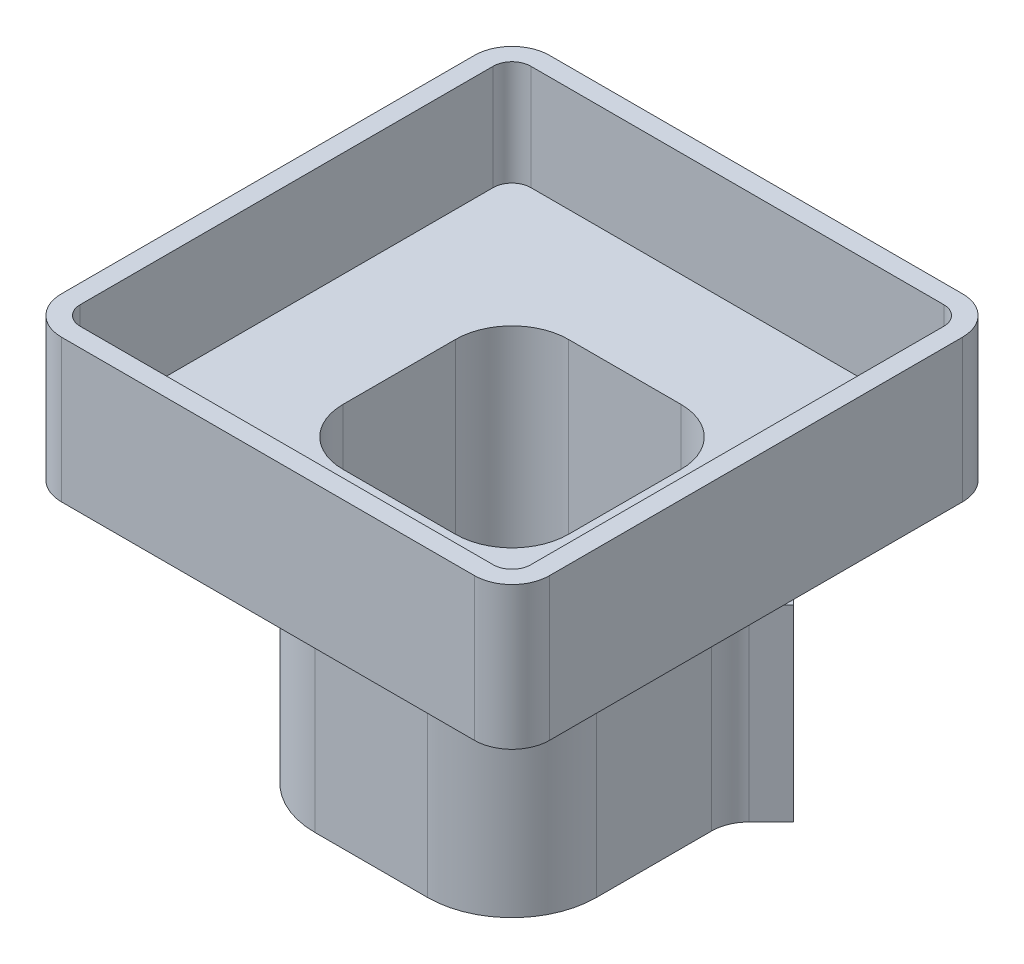
SolidWorks part; units mm, degrees
ref_plane "Front Plane" through (0, 0, 0) normal (0, 0, 1) x (1, 0, 0)
ref_plane "Top Plane" through (0, 0, 0) normal (0, 1, 0) x (1, 0, 0)
ref_plane "Right Plane" through (0, 0, 0) normal (1, 0, 0) x (0, 0, -1)
sketch "Sketch1" plane through (0, 0, 0) normal (0, 1, 0) x (1, 0, 0)
  line L1 (-3.75, 3.75) -> (3.75, 3.75)
  line L2 (-3.75, 3.75) -> (-3.75, -3.75)
  line L3 (-3.75, -3.75) -> (3.75, -3.75)
  line L4 (3.75, 3.75) -> (3.75, -3.75)
  line L5 (-3.75, 3.75) -> (3.75, -3.75) construction
  line L6 (-3.75, -3.75) -> (3.75, 3.75) construction
  dimension "D2" = 7.5
extrude "Boss-Extrude1" add sketch "Sketch1" along normal blind 7
sketch "Sketch2" plane through (0, 7, 0) normal (0, 1, 0) x (1, 0, 0)
  line L1 (6.5, 6.5) -> (-6.5, 6.5)
  line L2 (6.5, 6.5) -> (6.5, -6.5)
  line L3 (6.5, -6.5) -> (-6.5, -6.5)
  line L4 (-6.5, 6.5) -> (-6.5, -6.5)
  line L5 (6.5, 6.5) -> (-6.5, -6.5) construction
  line L6 (6.5, -6.5) -> (-6.5, 6.5) construction
  point P0 (0, 0)
  dimension "D1" = 13
  dimension "D2" = 13
extrude "Boss-Extrude2" add sketch "Sketch2" along normal blind 3.8
sketch "Sketch3" plane through (0, 0, 0) normal (0, -1, 0) x (1, 0, 0)
  line L1 (-3, -3) -> (3, -3)
  line L2 (-3, -3) -> (-3, 3)
  line L3 (-3, 3) -> (3, 3)
  line L4 (3, -3) -> (3, 3)
  line L5 (-3, -3) -> (3, 3) construction
  line L6 (-3, 3) -> (3, -3) construction
  dimension "D2" = 6
extrude "Cut-Extrude1" cut sketch "Sketch3" against normal through all
sketch "Sketch6" plane through (0, 10.8, 0) normal (0, 1, 0) x (1, 0, 0)
  line L1 (6, 6) -> (-6, 6)
  line L2 (6, 6) -> (6, -6)
  line L3 (6, -6) -> (-6, -6)
  line L4 (-6, 6) -> (-6, -6)
  line L5 (6, 6) -> (-6, -6) construction
  line L6 (6, -6) -> (-6, 6) construction
  point P0 (0, 0)
  dimension "D1" = 12
  dimension "D2" = 12
extrude "Cut-Extrude3" cut sketch "Sketch6" against normal offset from surface (2.8 mm away) 1 up to face at (0, 7, 0)
fillet "Fillet1" radius 0.5 4 edges at (-6, 9.4, -6) (6, 9.4, -6) (6, 9.4, 6) (-6, 9.4, 6)
sketch "Sketch12" plane through (0, 0, 0) normal (0, -1, 0) x (1, 0, 0)
  line L0 (4.6339, -2.8661) -> (3.75, -1.9822)
  line L1 (3.75, 3.75) -> (3.75, -3.75) construction
  line L2 (3.75, -1.9822) -> (1.9822, -3.75)
  line L3 (3.75, -3.75) -> (-3.75, -3.75) construction
  line L4 (1.9822, -3.75) -> (2.8661, -4.6339)
  line L5 (2.8661, -4.6339) -> (4.6339, -2.8661)
  dimension "D1" = 45
  dimension "D2" = 2.5
extrude "Boss-Extrude3" add sketch "Sketch12" against normal up to next
fillet "Fillet4" radius 1.5 4 edges at (-3, 4, -3) (-3, 4, 3) (3, 4, 3) (3, 4, -3)
fillet "Fillet2" radius 1 2 edges at (3.75, 3.5, -1.9822) (1.9822, 3.5, -3.75)
sketch "Sketch13" plane through (3.75, 0, -3.75) normal (0.7071, 0, -0.7071) x (-0.7071, 0, -0.7071)
  line L0 (0, 0) -> (0, 1.25) construction
  line L1 (1.25, 0) -> (-1.25, 0) construction
  line L2 (0, 1.25) -> (0, 3.75) construction
  dimension "D1" = 1.25
  dimension "D2" = 2.5
hole_wizard "Tap Drill for #0-80 Tap1" positions "Sketch15" profile "Sketch14" hole size "#0-80" standard "ANSI Inch"
sketch "Sketch15" plane through (3.75, 0, -3.75) normal (0.7071, 0, -0.7071) x (-0.7071, 0, -0.7071)
  point P0 (0, 1.25)
  point P3 (0, 3.75)
sketch "Sketch14" plane through (3.75, 1.25, -3.75) normal (0, 1, 0) x (-0.7071, 0, -0.7071)
  line L0 (0, 0) -> (0, 7.4679)
  line L1 (0, 7.4679) -> (0.5956, 7.11)
  line L2 (0.5956, 7.11) -> (0.5956, 0)
  line L5 (0.5956, 0) -> (0, 0)
  line L10 (0, 7.4679) -> (-0.5956, 7.11) construction
  line L11 (0, -6.35) -> (0, 107.95) construction
  dimension "Hole Dia." = 1.1913
  dimension "Hole Depth" = 7.11
  dimension "Drill Angle" = 118
fillet "Fillet5" radius 2.25 3 edges at (3.75, 3.5, 3.75) (-3.75, 3.5, 3.75) (-3.75, 3.5, -3.75)
sketch "Sketch16" plane through (3.75, 0, -3.75) normal (0.7071, 0, -0.7071) x (-0.7071, 0, -0.7071)
  line L0 (-1.25, 7) -> (-1.25, 0) construction
  line L1 (1.25, 7) -> (-1.25, 7)
  line L2 (1.25, 7) -> (1.25, 5)
  line L3 (1.25, 5) -> (-1.25, 5)
  line L4 (-1.25, 7) -> (-1.25, 5)
  line L6 (1.25, 0) -> (-1.25, 0) construction
  dimension "D1" = 5
extrude "Cut-Extrude4" cut sketch "Sketch16" against normal up to vertex (0.8358 mm away)
fillet "Fillet6" radius 1 4 edges at (-6.5, 8.9, 6.5) (-6.5, 8.9, -6.5) (6.5, 8.9, 6.5) (6.5, 8.9, -6.5)
